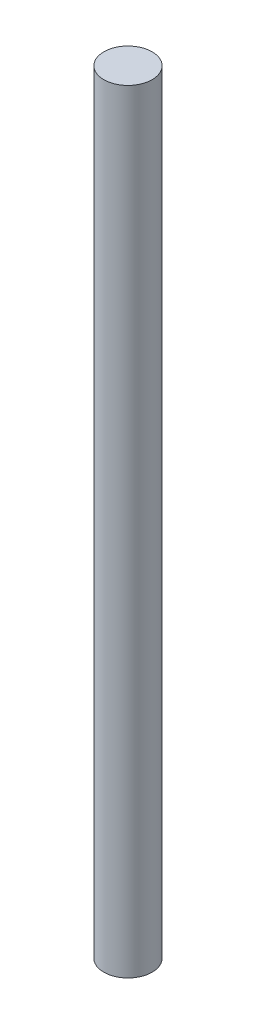
SolidWorks part; units mm, degrees
ref_plane "Front" through (0, 0, 0) normal (0, 0, 1) x (1, 0, 0)
ref_plane "Top" through (0, 0, 0) normal (0, 1, 0) x (1, 0, 0)
ref_plane "Right" through (0, 0, 0) normal (1, 0, 0) x (0, 0, -1)
sketch "Sketch1" plane through (0, 0, 0) normal (0, 1, 0) x (1, 0, 0)
  circle A0 centre (0, 0) radius 9.525
extrude "Boss-Extrude1" add sketch "Sketch1" along normal blind 304.8
